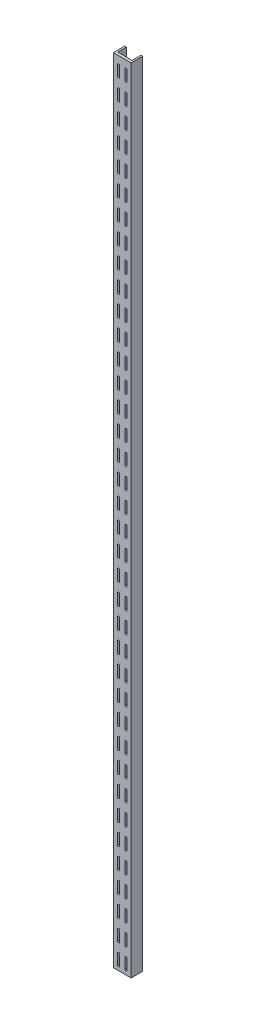
SolidWorks part; units mm, degrees
ref_plane "Front Plane" through (0, 0, 0) normal (0, 0, 1) x (1, 0, 0)
ref_plane "Top Plane" through (0, 0, 0) normal (0, 1, 0) x (1, 0, 0)
ref_plane "Right Plane" through (0, 0, 0) normal (1, 0, 0) x (0, 0, -1)
sketch "Sketch1" plane through (0, 0, 0) normal (0, 1, 0) x (1, 0, 0)
  line L0 (0, 0) -> (0, 17.7)
  line L1 (0, 17.7) -> (2.62, 17.7)
  line L2 (2.62, 17.7) -> (2.62, 4.15)
  line L3 (2.62, 4.15) -> (24.7, 4.15)
  line L4 (24.7, 4.15) -> (24.7, 17.7)
  line L5 (24.7, 17.7) -> (27.32, 17.7)
  line L6 (27.32, 17.7) -> (27.32, 0)
  line L7 (27.32, 0) -> (0, 0)
  line L8 (13.66, 4.15) -> (13.66, 0) construction
  dimension "D1" = 27.32
  dimension "D2" = 17.7
  dimension "D3" = 2.62
  dimension "D4" = 4.15
extrude "Boss-Extrude1" add sketch "Sketch1" along normal blind 1219.2
sketch "Sketch2" plane through (0, 0, -4.15) normal (0, 0, -1) x (-1, 0, 0)
  line L0 (-13.66, 1164.6545) -> (-13.66, 1127.3259) construction
  line L1 (-14.98, 1155.99) -> (-12.34, 1155.99)
  line L2 (-14.98, 1155.99) -> (-14.98, 1141.99)
  line L3 (-14.98, 1141.99) -> (-12.34, 1141.99)
  line L4 (-12.34, 1155.99) -> (-12.34, 1141.99)
  line L6 (-24.7, 1219.2) -> (-2.62, 1219.2) construction
  line L7 (-14.98, 1130.89) -> (-14.98, 1116.89)
  line L8 (-14.98, 1130.89) -> (-12.34, 1130.89)
  line L9 (-12.34, 1130.89) -> (-12.34, 1116.89)
  line L10 (-14.98, 1116.89) -> (-12.34, 1116.89)
  line L11 (-14.98, 1105.79) -> (-14.98, 1091.79)
  line L12 (-14.98, 1105.79) -> (-12.34, 1105.79)
  line L13 (-12.34, 1105.79) -> (-12.34, 1091.79)
  line L14 (-14.98, 1091.79) -> (-12.34, 1091.79)
  line L15 (-14.98, 1080.69) -> (-14.98, 1066.69)
  line L16 (-14.98, 1080.69) -> (-12.34, 1080.69)
  line L17 (-12.34, 1080.69) -> (-12.34, 1066.69)
  line L18 (-14.98, 1066.69) -> (-12.34, 1066.69)
  line L19 (-14.98, 1055.59) -> (-14.98, 1041.59)
  line L20 (-14.98, 1055.59) -> (-12.34, 1055.59)
  line L21 (-12.34, 1055.59) -> (-12.34, 1041.59)
  line L22 (-14.98, 1041.59) -> (-12.34, 1041.59)
  line L23 (-14.98, 1030.49) -> (-14.98, 1016.49)
  line L24 (-14.98, 1030.49) -> (-12.34, 1030.49)
  line L25 (-12.34, 1030.49) -> (-12.34, 1016.49)
  line L26 (-14.98, 1016.49) -> (-12.34, 1016.49)
  line L27 (-14.98, 1005.39) -> (-14.98, 991.39)
  line L28 (-14.98, 1005.39) -> (-12.34, 1005.39)
  line L29 (-12.34, 1005.39) -> (-12.34, 991.39)
  line L30 (-14.98, 991.39) -> (-12.34, 991.39)
  line L31 (-14.98, 980.29) -> (-14.98, 966.29)
  line L32 (-14.98, 980.29) -> (-12.34, 980.29)
  line L33 (-12.34, 980.29) -> (-12.34, 966.29)
  line L34 (-14.98, 966.29) -> (-12.34, 966.29)
  line L35 (-14.98, 955.19) -> (-14.98, 941.19)
  line L36 (-14.98, 955.19) -> (-12.34, 955.19)
  line L37 (-12.34, 955.19) -> (-12.34, 941.19)
  line L38 (-14.98, 941.19) -> (-12.34, 941.19)
  line L39 (-14.98, 930.09) -> (-14.98, 916.09)
  line L40 (-14.98, 930.09) -> (-12.34, 930.09)
  line L41 (-12.34, 930.09) -> (-12.34, 916.09)
  line L42 (-14.98, 916.09) -> (-12.34, 916.09)
  line L43 (-14.98, 904.99) -> (-14.98, 890.99)
  line L44 (-14.98, 904.99) -> (-12.34, 904.99)
  line L45 (-12.34, 904.99) -> (-12.34, 890.99)
  line L46 (-14.98, 890.99) -> (-12.34, 890.99)
  line L47 (-14.98, 879.89) -> (-14.98, 865.89)
  line L48 (-14.98, 879.89) -> (-12.34, 879.89)
  line L49 (-12.34, 879.89) -> (-12.34, 865.89)
  line L50 (-14.98, 865.89) -> (-12.34, 865.89)
  line L51 (-14.98, 854.79) -> (-14.98, 840.79)
  line L52 (-14.98, 854.79) -> (-12.34, 854.79)
  line L53 (-12.34, 854.79) -> (-12.34, 840.79)
  line L54 (-14.98, 840.79) -> (-12.34, 840.79)
  line L55 (-14.98, 829.69) -> (-14.98, 815.69)
  line L56 (-14.98, 829.69) -> (-12.34, 829.69)
  line L57 (-12.34, 829.69) -> (-12.34, 815.69)
  line L58 (-14.98, 815.69) -> (-12.34, 815.69)
  line L59 (-14.98, 804.59) -> (-14.98, 790.59)
  line L60 (-14.98, 804.59) -> (-12.34, 804.59)
  line L61 (-12.34, 804.59) -> (-12.34, 790.59)
  line L62 (-14.98, 790.59) -> (-12.34, 790.59)
  line L63 (-14.98, 779.49) -> (-14.98, 765.49)
  line L64 (-14.98, 779.49) -> (-12.34, 779.49)
  line L65 (-12.34, 779.49) -> (-12.34, 765.49)
  line L66 (-14.98, 765.49) -> (-12.34, 765.49)
  line L67 (-14.98, 754.39) -> (-14.98, 740.39)
  line L68 (-14.98, 754.39) -> (-12.34, 754.39)
  line L69 (-12.34, 754.39) -> (-12.34, 740.39)
  line L70 (-14.98, 740.39) -> (-12.34, 740.39)
  line L71 (-14.98, 729.29) -> (-14.98, 715.29)
  line L72 (-14.98, 729.29) -> (-12.34, 729.29)
  line L73 (-12.34, 729.29) -> (-12.34, 715.29)
  line L74 (-14.98, 715.29) -> (-12.34, 715.29)
  line L75 (-14.98, 704.19) -> (-14.98, 690.19)
  line L76 (-14.98, 704.19) -> (-12.34, 704.19)
  line L77 (-12.34, 704.19) -> (-12.34, 690.19)
  line L78 (-14.98, 690.19) -> (-12.34, 690.19)
  line L79 (-14.98, 679.09) -> (-14.98, 665.09)
  line L80 (-14.98, 679.09) -> (-12.34, 679.09)
  line L81 (-12.34, 679.09) -> (-12.34, 665.09)
  line L82 (-14.98, 665.09) -> (-12.34, 665.09)
  line L83 (-14.98, 653.99) -> (-14.98, 639.99)
  line L84 (-14.98, 653.99) -> (-12.34, 653.99)
  line L85 (-12.34, 653.99) -> (-12.34, 639.99)
  line L86 (-14.98, 639.99) -> (-12.34, 639.99)
  line L87 (-14.98, 628.89) -> (-14.98, 614.89)
  line L88 (-14.98, 628.89) -> (-12.34, 628.89)
  line L89 (-12.34, 628.89) -> (-12.34, 614.89)
  line L90 (-14.98, 614.89) -> (-12.34, 614.89)
  line L91 (-14.98, 603.79) -> (-14.98, 589.79)
  line L92 (-14.98, 603.79) -> (-12.34, 603.79)
  line L93 (-12.34, 603.79) -> (-12.34, 589.79)
  line L94 (-14.98, 589.79) -> (-12.34, 589.79)
  line L95 (-14.98, 578.69) -> (-14.98, 564.69)
  line L96 (-14.98, 578.69) -> (-12.34, 578.69)
  line L97 (-12.34, 578.69) -> (-12.34, 564.69)
  line L98 (-14.98, 564.69) -> (-12.34, 564.69)
  line L99 (-14.98, 553.59) -> (-14.98, 539.59)
  line L100 (-14.98, 553.59) -> (-12.34, 553.59)
  line L101 (-12.34, 553.59) -> (-12.34, 539.59)
  line L102 (-14.98, 539.59) -> (-12.34, 539.59)
  line L103 (-14.98, 528.49) -> (-14.98, 514.49)
  line L104 (-14.98, 528.49) -> (-12.34, 528.49)
  line L105 (-12.34, 528.49) -> (-12.34, 514.49)
  line L106 (-14.98, 514.49) -> (-12.34, 514.49)
  line L107 (-14.98, 503.39) -> (-14.98, 489.39)
  line L108 (-14.98, 503.39) -> (-12.34, 503.39)
  line L109 (-12.34, 503.39) -> (-12.34, 489.39)
  line L110 (-14.98, 489.39) -> (-12.34, 489.39)
  line L111 (-14.98, 478.29) -> (-14.98, 464.29)
  line L112 (-14.98, 478.29) -> (-12.34, 478.29)
  line L113 (-12.34, 478.29) -> (-12.34, 464.29)
  line L114 (-14.98, 464.29) -> (-12.34, 464.29)
  line L115 (-14.98, 453.19) -> (-14.98, 439.19)
  line L116 (-14.98, 453.19) -> (-12.34, 453.19)
  line L117 (-12.34, 453.19) -> (-12.34, 439.19)
  line L118 (-14.98, 439.19) -> (-12.34, 439.19)
  line L119 (-14.98, 428.09) -> (-14.98, 414.09)
  line L120 (-14.98, 428.09) -> (-12.34, 428.09)
  line L121 (-12.34, 428.09) -> (-12.34, 414.09)
  line L122 (-14.98, 414.09) -> (-12.34, 414.09)
  line L123 (-14.98, 402.99) -> (-14.98, 388.99)
  line L124 (-14.98, 402.99) -> (-12.34, 402.99)
  line L125 (-12.34, 402.99) -> (-12.34, 388.99)
  line L126 (-14.98, 388.99) -> (-12.34, 388.99)
  line L127 (-14.98, 377.89) -> (-14.98, 363.89)
  line L128 (-14.98, 377.89) -> (-12.34, 377.89)
  line L129 (-12.34, 377.89) -> (-12.34, 363.89)
  line L130 (-14.98, 363.89) -> (-12.34, 363.89)
  line L131 (-14.98, 352.79) -> (-14.98, 338.79)
  line L132 (-14.98, 352.79) -> (-12.34, 352.79)
  line L133 (-12.34, 352.79) -> (-12.34, 338.79)
  line L134 (-14.98, 338.79) -> (-12.34, 338.79)
  line L135 (-14.98, 327.69) -> (-14.98, 313.69)
  line L136 (-14.98, 327.69) -> (-12.34, 327.69)
  line L137 (-12.34, 327.69) -> (-12.34, 313.69)
  line L138 (-14.98, 313.69) -> (-12.34, 313.69)
  line L139 (-14.98, 302.59) -> (-14.98, 288.59)
  line L140 (-14.98, 302.59) -> (-12.34, 302.59)
  line L141 (-12.34, 302.59) -> (-12.34, 288.59)
  line L142 (-14.98, 288.59) -> (-12.34, 288.59)
  line L143 (-14.98, 277.49) -> (-14.98, 263.49)
  line L144 (-14.98, 277.49) -> (-12.34, 277.49)
  line L145 (-12.34, 277.49) -> (-12.34, 263.49)
  line L146 (-14.98, 263.49) -> (-12.34, 263.49)
  line L147 (-14.98, 252.39) -> (-14.98, 238.39)
  line L148 (-14.98, 252.39) -> (-12.34, 252.39)
  line L149 (-12.34, 252.39) -> (-12.34, 238.39)
  line L150 (-14.98, 238.39) -> (-12.34, 238.39)
  line L151 (-14.98, 227.29) -> (-14.98, 213.29)
  line L152 (-14.98, 227.29) -> (-12.34, 227.29)
  line L153 (-12.34, 227.29) -> (-12.34, 213.29)
  line L154 (-14.98, 213.29) -> (-12.34, 213.29)
  line L155 (-14.98, 202.19) -> (-14.98, 188.19)
  line L156 (-14.98, 202.19) -> (-12.34, 202.19)
  line L157 (-12.34, 202.19) -> (-12.34, 188.19)
  line L158 (-14.98, 188.19) -> (-12.34, 188.19)
  line L159 (-14.98, 177.09) -> (-14.98, 163.09)
  line L160 (-14.98, 177.09) -> (-12.34, 177.09)
  line L161 (-12.34, 177.09) -> (-12.34, 163.09)
  line L162 (-14.98, 163.09) -> (-12.34, 163.09)
  line L163 (-14.98, 151.99) -> (-14.98, 137.99)
  line L164 (-14.98, 151.99) -> (-12.34, 151.99)
  line L165 (-12.34, 151.99) -> (-12.34, 137.99)
  line L166 (-14.98, 137.99) -> (-12.34, 137.99)
  line L167 (-14.98, 126.89) -> (-14.98, 112.89)
  line L168 (-14.98, 126.89) -> (-12.34, 126.89)
  line L169 (-12.34, 126.89) -> (-12.34, 112.89)
  line L170 (-14.98, 112.89) -> (-12.34, 112.89)
  line L171 (-14.98, 101.79) -> (-14.98, 87.79)
  line L172 (-14.98, 101.79) -> (-12.34, 101.79)
  line L173 (-12.34, 101.79) -> (-12.34, 87.79)
  line L174 (-14.98, 87.79) -> (-12.34, 87.79)
  line L175 (-14.98, 76.69) -> (-14.98, 62.69)
  line L176 (-14.98, 76.69) -> (-12.34, 76.69)
  line L177 (-12.34, 76.69) -> (-12.34, 62.69)
  line L178 (-14.98, 62.69) -> (-12.34, 62.69)
  line L179 (-14.98, 51.59) -> (-14.98, 37.59)
  line L180 (-14.98, 51.59) -> (-12.34, 51.59)
  line L181 (-12.34, 51.59) -> (-12.34, 37.59)
  line L182 (-14.98, 37.59) -> (-12.34, 37.59)
  line L183 (-14.98, 26.49) -> (-14.98, 12.49)
  line L184 (-14.98, 26.49) -> (-12.34, 26.49)
  line L185 (-12.34, 26.49) -> (-12.34, 12.49)
  line L186 (-14.98, 12.49) -> (-12.34, 12.49)
  point P5 (-13.66, 1155.99)
  point P9 (-13.66, 1219.2)
  dimension "D1" = 2.64
  dimension "D2" = 63.21
  dimension "D3" = 14
  dimension "D4" = 46
  dimension "D5" = 11.1
extrude "Cut-Extrude1" [suppressed] cut sketch "Sketch2" against normal through all
sketch "Sketch3" plane through (0, 0, -4.15) normal (0, 0, -1) x (-1, 0, 0)
  line L0 (-13.66, 1225.2426) -> (-13.66, 1213.1338) construction
  line L2 (-24.7, 1219.2) -> (-2.62, 1219.2) construction
  circle A0 centre (-13.66, 1210.325) radius 2.195
  circle A1 centre (-13.66, 830.595) radius 2.195
  circle A2 centre (-13.66, 563.895) radius 2.195
  circle A3 centre (-13.66, 297.195) radius 2.195
  circle A4 centre (-13.66, 30.495) radius 2.195
  point P3 (-13.66, 1219.1882)
  point P5 (-13.66, 1219.2)
  dimension "D1" = 4.39
  dimension "D3" = 379.73
  dimension "D4" = 4.39
  dimension "D2" = 8.875
  dimension "D5" = 4
extrude "Cut-Extrude2" [suppressed] cut sketch "Sketch3" against normal through all
sketch "Sketch4" plane through (0, 0, -4.15) normal (0, 0, -1) x (-1, 0, 0)
  line L0 (-19.4, 1206.81) -> (-19.4, 1190.81) construction
  line L1 (-17.9, 1206.81) -> (-17.9, 1190.81)
  line L2 (-20.9, 1206.81) -> (-20.9, 1190.81)
  line L3 (-13.66, 1219.2) -> (-13.66, 0) construction
  line L4 (-24.7, 1219.2) -> (-2.62, 1219.2) construction
  line L5 (-24.7, 0) -> (-2.62, 0) construction
  line L6 (-20.9, 1174.81) -> (-20.9, 1158.81)
  line L7 (-17.9, 1174.81) -> (-17.9, 1158.81)
  line L8 (-19.4, 1174.81) -> (-19.4, 1158.81) construction
  line L9 (-20.9, 1142.81) -> (-20.9, 1126.81)
  line L10 (-17.9, 1142.81) -> (-17.9, 1126.81)
  line L11 (-19.4, 1142.81) -> (-19.4, 1126.81) construction
  line L12 (-20.9, 1110.81) -> (-20.9, 1094.81)
  line L13 (-17.9, 1110.81) -> (-17.9, 1094.81)
  line L14 (-19.4, 1110.81) -> (-19.4, 1094.81) construction
  line L15 (-20.9, 1078.81) -> (-20.9, 1062.81)
  line L16 (-17.9, 1078.81) -> (-17.9, 1062.81)
  line L17 (-19.4, 1078.81) -> (-19.4, 1062.81) construction
  line L18 (-20.9, 1046.81) -> (-20.9, 1030.81)
  line L19 (-17.9, 1046.81) -> (-17.9, 1030.81)
  line L20 (-19.4, 1046.81) -> (-19.4, 1030.81) construction
  line L21 (-20.9, 1014.81) -> (-20.9, 998.81)
  line L22 (-17.9, 1014.81) -> (-17.9, 998.81)
  line L23 (-19.4, 1014.81) -> (-19.4, 998.81) construction
  line L24 (-20.9, 982.81) -> (-20.9, 966.81)
  line L25 (-17.9, 982.81) -> (-17.9, 966.81)
  line L26 (-19.4, 982.81) -> (-19.4, 966.81) construction
  line L27 (-20.9, 950.81) -> (-20.9, 934.81)
  line L28 (-17.9, 950.81) -> (-17.9, 934.81)
  line L29 (-19.4, 950.81) -> (-19.4, 934.81) construction
  line L30 (-20.9, 918.81) -> (-20.9, 902.81)
  line L31 (-17.9, 918.81) -> (-17.9, 902.81)
  line L32 (-19.4, 918.81) -> (-19.4, 902.81) construction
  line L33 (-20.9, 886.81) -> (-20.9, 870.81)
  line L34 (-17.9, 886.81) -> (-17.9, 870.81)
  line L35 (-19.4, 886.81) -> (-19.4, 870.81) construction
  line L36 (-20.9, 854.81) -> (-20.9, 838.81)
  line L37 (-17.9, 854.81) -> (-17.9, 838.81)
  line L38 (-19.4, 854.81) -> (-19.4, 838.81) construction
  line L39 (-20.9, 822.81) -> (-20.9, 806.81)
  line L40 (-17.9, 822.81) -> (-17.9, 806.81)
  line L41 (-19.4, 822.81) -> (-19.4, 806.81) construction
  line L42 (-20.9, 790.81) -> (-20.9, 774.81)
  line L43 (-17.9, 790.81) -> (-17.9, 774.81)
  line L44 (-19.4, 790.81) -> (-19.4, 774.81) construction
  line L45 (-20.9, 758.81) -> (-20.9, 742.81)
  line L46 (-17.9, 758.81) -> (-17.9, 742.81)
  line L47 (-19.4, 758.81) -> (-19.4, 742.81) construction
  line L48 (-20.9, 726.81) -> (-20.9, 710.81)
  line L49 (-17.9, 726.81) -> (-17.9, 710.81)
  line L50 (-19.4, 726.81) -> (-19.4, 710.81) construction
  line L51 (-20.9, 694.81) -> (-20.9, 678.81)
  line L52 (-17.9, 694.81) -> (-17.9, 678.81)
  line L53 (-19.4, 694.81) -> (-19.4, 678.81) construction
  line L54 (-20.9, 662.81) -> (-20.9, 646.81)
  line L55 (-17.9, 662.81) -> (-17.9, 646.81)
  line L56 (-19.4, 662.81) -> (-19.4, 646.81) construction
  line L57 (-20.9, 630.81) -> (-20.9, 614.81)
  line L58 (-17.9, 630.81) -> (-17.9, 614.81)
  line L59 (-19.4, 630.81) -> (-19.4, 614.81) construction
  line L60 (-20.9, 598.81) -> (-20.9, 582.81)
  line L61 (-17.9, 598.81) -> (-17.9, 582.81)
  line L62 (-19.4, 598.81) -> (-19.4, 582.81) construction
  line L63 (-20.9, 566.81) -> (-20.9, 550.81)
  line L64 (-17.9, 566.81) -> (-17.9, 550.81)
  line L65 (-19.4, 566.81) -> (-19.4, 550.81) construction
  line L66 (-20.9, 534.81) -> (-20.9, 518.81)
  line L67 (-17.9, 534.81) -> (-17.9, 518.81)
  line L68 (-19.4, 534.81) -> (-19.4, 518.81) construction
  line L69 (-20.9, 502.81) -> (-20.9, 486.81)
  line L70 (-17.9, 502.81) -> (-17.9, 486.81)
  line L71 (-19.4, 502.81) -> (-19.4, 486.81) construction
  line L72 (-20.9, 470.81) -> (-20.9, 454.81)
  line L73 (-17.9, 470.81) -> (-17.9, 454.81)
  line L74 (-19.4, 470.81) -> (-19.4, 454.81) construction
  line L75 (-20.9, 438.81) -> (-20.9, 422.81)
  line L76 (-17.9, 438.81) -> (-17.9, 422.81)
  line L77 (-19.4, 438.81) -> (-19.4, 422.81) construction
  line L78 (-20.9, 406.81) -> (-20.9, 390.81)
  line L79 (-17.9, 406.81) -> (-17.9, 390.81)
  line L80 (-19.4, 406.81) -> (-19.4, 390.81) construction
  line L81 (-20.9, 374.81) -> (-20.9, 358.81)
  line L82 (-17.9, 374.81) -> (-17.9, 358.81)
  line L83 (-19.4, 374.81) -> (-19.4, 358.81) construction
  line L84 (-20.9, 342.81) -> (-20.9, 326.81)
  line L85 (-17.9, 342.81) -> (-17.9, 326.81)
  line L86 (-19.4, 342.81) -> (-19.4, 326.81) construction
  line L87 (-20.9, 310.81) -> (-20.9, 294.81)
  line L88 (-17.9, 310.81) -> (-17.9, 294.81)
  line L89 (-19.4, 310.81) -> (-19.4, 294.81) construction
  line L90 (-20.9, 278.81) -> (-20.9, 262.81)
  line L91 (-17.9, 278.81) -> (-17.9, 262.81)
  line L92 (-19.4, 278.81) -> (-19.4, 262.81) construction
  line L93 (-20.9, 246.81) -> (-20.9, 230.81)
  line L94 (-17.9, 246.81) -> (-17.9, 230.81)
  line L95 (-19.4, 246.81) -> (-19.4, 230.81) construction
  line L96 (-20.9, 214.81) -> (-20.9, 198.81)
  line L97 (-17.9, 214.81) -> (-17.9, 198.81)
  line L98 (-19.4, 214.81) -> (-19.4, 198.81) construction
  line L99 (-20.9, 182.81) -> (-20.9, 166.81)
  line L100 (-17.9, 182.81) -> (-17.9, 166.81)
  line L101 (-19.4, 182.81) -> (-19.4, 166.81) construction
  line L102 (-20.9, 150.81) -> (-20.9, 134.81)
  line L103 (-17.9, 150.81) -> (-17.9, 134.81)
  line L104 (-19.4, 150.81) -> (-19.4, 134.81) construction
  line L105 (-20.9, 118.81) -> (-20.9, 102.81)
  line L106 (-17.9, 118.81) -> (-17.9, 102.81)
  line L107 (-19.4, 118.81) -> (-19.4, 102.81) construction
  line L108 (-20.9, 86.81) -> (-20.9, 70.81)
  line L109 (-17.9, 86.81) -> (-17.9, 70.81)
  line L110 (-19.4, 86.81) -> (-19.4, 70.81) construction
  line L111 (-20.9, 54.81) -> (-20.9, 38.81)
  line L112 (-17.9, 54.81) -> (-17.9, 38.81)
  line L113 (-19.4, 54.81) -> (-19.4, 38.81) construction
  line L114 (-20.9, 22.81) -> (-20.9, 6.81)
  line L115 (-17.9, 22.81) -> (-17.9, 6.81)
  line L116 (-19.4, 22.81) -> (-19.4, 6.81) construction
  line L117 (-7.92, 758.81) -> (-7.92, 742.81) construction
  line L118 (-9.42, 758.81) -> (-9.42, 742.81)
  line L119 (-6.42, 758.81) -> (-6.42, 742.81)
  line L120 (-7.92, 790.81) -> (-7.92, 774.81) construction
  line L121 (-9.42, 790.81) -> (-9.42, 774.81)
  line L122 (-6.42, 790.81) -> (-6.42, 774.81)
  line L123 (-7.92, 822.81) -> (-7.92, 806.81) construction
  line L124 (-9.42, 822.81) -> (-9.42, 806.81)
  line L125 (-6.42, 822.81) -> (-6.42, 806.81)
  line L126 (-7.92, 854.81) -> (-7.92, 838.81) construction
  line L127 (-9.42, 854.81) -> (-9.42, 838.81)
  line L128 (-6.42, 854.81) -> (-6.42, 838.81)
  line L129 (-7.92, 886.81) -> (-7.92, 870.81) construction
  line L130 (-9.42, 886.81) -> (-9.42, 870.81)
  line L131 (-6.42, 886.81) -> (-6.42, 870.81)
  line L132 (-7.92, 918.81) -> (-7.92, 902.81) construction
  line L133 (-9.42, 918.81) -> (-9.42, 902.81)
  line L134 (-6.42, 918.81) -> (-6.42, 902.81)
  line L135 (-7.92, 950.81) -> (-7.92, 934.81) construction
  line L136 (-9.42, 950.81) -> (-9.42, 934.81)
  line L137 (-6.42, 950.81) -> (-6.42, 934.81)
  line L138 (-7.92, 982.81) -> (-7.92, 966.81) construction
  line L139 (-9.42, 982.81) -> (-9.42, 966.81)
  line L140 (-6.42, 982.81) -> (-6.42, 966.81)
  line L141 (-7.92, 1014.81) -> (-7.92, 998.81) construction
  line L142 (-9.42, 1014.81) -> (-9.42, 998.81)
  line L143 (-6.42, 1014.81) -> (-6.42, 998.81)
  line L144 (-7.92, 1046.81) -> (-7.92, 1030.81) construction
  line L145 (-9.42, 1046.81) -> (-9.42, 1030.81)
  line L146 (-6.42, 1046.81) -> (-6.42, 1030.81)
  line L147 (-7.92, 1078.81) -> (-7.92, 1062.81) construction
  line L148 (-9.42, 1078.81) -> (-9.42, 1062.81)
  line L149 (-6.42, 1078.81) -> (-6.42, 1062.81)
  line L150 (-7.92, 1110.81) -> (-7.92, 1094.81) construction
  line L151 (-9.42, 1110.81) -> (-9.42, 1094.81)
  line L152 (-6.42, 1110.81) -> (-6.42, 1094.81)
  line L153 (-7.92, 1142.81) -> (-7.92, 1126.81) construction
  line L154 (-9.42, 1142.81) -> (-9.42, 1126.81)
  line L155 (-6.42, 1142.81) -> (-6.42, 1126.81)
  line L156 (-7.92, 1174.81) -> (-7.92, 1158.81) construction
  line L157 (-9.42, 1174.81) -> (-9.42, 1158.81)
  line L158 (-6.42, 1174.81) -> (-6.42, 1158.81)
  line L159 (-7.92, 1206.81) -> (-7.92, 1190.81) construction
  line L160 (-9.42, 1206.81) -> (-9.42, 1190.81)
  line L161 (-6.42, 1206.81) -> (-6.42, 1190.81)
  line L162 (-7.92, 406.81) -> (-7.92, 390.81) construction
  line L163 (-9.42, 406.81) -> (-9.42, 390.81)
  line L164 (-6.42, 406.81) -> (-6.42, 390.81)
  line L165 (-7.92, 438.81) -> (-7.92, 422.81) construction
  line L166 (-9.42, 438.81) -> (-9.42, 422.81)
  line L167 (-6.42, 438.81) -> (-6.42, 422.81)
  line L168 (-7.92, 470.81) -> (-7.92, 454.81) construction
  line L169 (-9.42, 470.81) -> (-9.42, 454.81)
  line L170 (-6.42, 470.81) -> (-6.42, 454.81)
  line L171 (-7.92, 502.81) -> (-7.92, 486.81) construction
  line L172 (-9.42, 502.81) -> (-9.42, 486.81)
  line L173 (-6.42, 502.81) -> (-6.42, 486.81)
  line L174 (-7.92, 534.81) -> (-7.92, 518.81) construction
  line L175 (-9.42, 534.81) -> (-9.42, 518.81)
  line L176 (-6.42, 534.81) -> (-6.42, 518.81)
  line L177 (-7.92, 566.81) -> (-7.92, 550.81) construction
  line L178 (-9.42, 566.81) -> (-9.42, 550.81)
  line L179 (-6.42, 566.81) -> (-6.42, 550.81)
  line L180 (-7.92, 598.81) -> (-7.92, 582.81) construction
  line L181 (-9.42, 598.81) -> (-9.42, 582.81)
  line L182 (-6.42, 598.81) -> (-6.42, 582.81)
  line L183 (-7.92, 630.81) -> (-7.92, 614.81) construction
  line L184 (-9.42, 630.81) -> (-9.42, 614.81)
  line L185 (-6.42, 630.81) -> (-6.42, 614.81)
  line L186 (-7.92, 662.81) -> (-7.92, 646.81) construction
  line L187 (-9.42, 662.81) -> (-9.42, 646.81)
  line L188 (-6.42, 662.81) -> (-6.42, 646.81)
  line L189 (-7.92, 694.81) -> (-7.92, 678.81) construction
  line L190 (-9.42, 694.81) -> (-9.42, 678.81)
  line L191 (-6.42, 694.81) -> (-6.42, 678.81)
  line L192 (-7.92, 726.81) -> (-7.92, 710.81) construction
  line L193 (-9.42, 726.81) -> (-9.42, 710.81)
  line L194 (-6.42, 726.81) -> (-6.42, 710.81)
  line L195 (-7.92, 374.81) -> (-7.92, 358.81) construction
  line L196 (-9.42, 374.81) -> (-9.42, 358.81)
  line L197 (-6.42, 374.81) -> (-6.42, 358.81)
  line L198 (-7.92, 342.81) -> (-7.92, 326.81) construction
  line L199 (-9.42, 342.81) -> (-9.42, 326.81)
  line L200 (-6.42, 342.81) -> (-6.42, 326.81)
  line L201 (-7.92, 310.81) -> (-7.92, 294.81) construction
  line L202 (-9.42, 310.81) -> (-9.42, 294.81)
  line L203 (-6.42, 310.81) -> (-6.42, 294.81)
  line L204 (-7.92, 278.81) -> (-7.92, 262.81) construction
  line L205 (-9.42, 278.81) -> (-9.42, 262.81)
  line L206 (-6.42, 278.81) -> (-6.42, 262.81)
  line L207 (-7.92, 246.81) -> (-7.92, 230.81) construction
  line L208 (-9.42, 246.81) -> (-9.42, 230.81)
  line L209 (-6.42, 246.81) -> (-6.42, 230.81)
  line L210 (-7.92, 214.81) -> (-7.92, 198.81) construction
  line L211 (-9.42, 214.81) -> (-9.42, 198.81)
  line L212 (-6.42, 214.81) -> (-6.42, 198.81)
  line L213 (-7.92, 182.81) -> (-7.92, 166.81) construction
  line L214 (-9.42, 182.81) -> (-9.42, 166.81)
  line L215 (-6.42, 182.81) -> (-6.42, 166.81)
  line L216 (-7.92, 150.81) -> (-7.92, 134.81) construction
  line L217 (-9.42, 150.81) -> (-9.42, 134.81)
  line L218 (-6.42, 150.81) -> (-6.42, 134.81)
  line L219 (-7.92, 118.81) -> (-7.92, 102.81) construction
  line L220 (-9.42, 118.81) -> (-9.42, 102.81)
  line L221 (-6.42, 118.81) -> (-6.42, 102.81)
  line L222 (-7.92, 86.81) -> (-7.92, 70.81) construction
  line L223 (-9.42, 86.81) -> (-9.42, 70.81)
  line L224 (-6.42, 86.81) -> (-6.42, 70.81)
  line L225 (-7.92, 54.81) -> (-7.92, 38.81) construction
  line L226 (-9.42, 54.81) -> (-9.42, 38.81)
  line L227 (-6.42, 54.81) -> (-6.42, 38.81)
  line L228 (-7.92, 22.81) -> (-7.92, 6.81) construction
  line L229 (-9.42, 22.81) -> (-9.42, 6.81)
  line L230 (-6.42, 22.81) -> (-6.42, 6.81)
  arc A0 (-17.9, 1206.81) -> (-20.9, 1206.81) centre (-19.4, 1206.81) ccw
  arc A1 (-20.9, 1190.81) -> (-17.9, 1190.81) centre (-19.4, 1190.81) ccw
  arc A2 (-17.9, 1174.81) -> (-20.9, 1174.81) centre (-19.4, 1174.81) ccw
  arc A3 (-20.9, 1158.81) -> (-17.9, 1158.81) centre (-19.4, 1158.81) ccw
  arc A4 (-17.9, 1142.81) -> (-20.9, 1142.81) centre (-19.4, 1142.81) ccw
  arc A5 (-20.9, 1126.81) -> (-17.9, 1126.81) centre (-19.4, 1126.81) ccw
  arc A6 (-17.9, 1110.81) -> (-20.9, 1110.81) centre (-19.4, 1110.81) ccw
  arc A7 (-20.9, 1094.81) -> (-17.9, 1094.81) centre (-19.4, 1094.81) ccw
  arc A8 (-17.9, 1078.81) -> (-20.9, 1078.81) centre (-19.4, 1078.81) ccw
  arc A9 (-20.9, 1062.81) -> (-17.9, 1062.81) centre (-19.4, 1062.81) ccw
  arc A10 (-17.9, 1046.81) -> (-20.9, 1046.81) centre (-19.4, 1046.81) ccw
  arc A11 (-20.9, 1030.81) -> (-17.9, 1030.81) centre (-19.4, 1030.81) ccw
  arc A12 (-17.9, 1014.81) -> (-20.9, 1014.81) centre (-19.4, 1014.81) ccw
  arc A13 (-20.9, 998.81) -> (-17.9, 998.81) centre (-19.4, 998.81) ccw
  arc A14 (-17.9, 982.81) -> (-20.9, 982.81) centre (-19.4, 982.81) ccw
  arc A15 (-20.9, 966.81) -> (-17.9, 966.81) centre (-19.4, 966.81) ccw
  arc A16 (-17.9, 950.81) -> (-20.9, 950.81) centre (-19.4, 950.81) ccw
  arc A17 (-20.9, 934.81) -> (-17.9, 934.81) centre (-19.4, 934.81) ccw
  arc A18 (-17.9, 918.81) -> (-20.9, 918.81) centre (-19.4, 918.81) ccw
  arc A19 (-20.9, 902.81) -> (-17.9, 902.81) centre (-19.4, 902.81) ccw
  arc A20 (-17.9, 886.81) -> (-20.9, 886.81) centre (-19.4, 886.81) ccw
  arc A21 (-20.9, 870.81) -> (-17.9, 870.81) centre (-19.4, 870.81) ccw
  arc A22 (-17.9, 854.81) -> (-20.9, 854.81) centre (-19.4, 854.81) ccw
  arc A23 (-20.9, 838.81) -> (-17.9, 838.81) centre (-19.4, 838.81) ccw
  arc A24 (-17.9, 822.81) -> (-20.9, 822.81) centre (-19.4, 822.81) ccw
  arc A25 (-20.9, 806.81) -> (-17.9, 806.81) centre (-19.4, 806.81) ccw
  arc A26 (-17.9, 790.81) -> (-20.9, 790.81) centre (-19.4, 790.81) ccw
  arc A27 (-20.9, 774.81) -> (-17.9, 774.81) centre (-19.4, 774.81) ccw
  arc A28 (-17.9, 758.81) -> (-20.9, 758.81) centre (-19.4, 758.81) ccw
  arc A29 (-20.9, 742.81) -> (-17.9, 742.81) centre (-19.4, 742.81) ccw
  arc A30 (-17.9, 726.81) -> (-20.9, 726.81) centre (-19.4, 726.81) ccw
  arc A31 (-20.9, 710.81) -> (-17.9, 710.81) centre (-19.4, 710.81) ccw
  arc A32 (-17.9, 694.81) -> (-20.9, 694.81) centre (-19.4, 694.81) ccw
  arc A33 (-20.9, 678.81) -> (-17.9, 678.81) centre (-19.4, 678.81) ccw
  arc A34 (-17.9, 662.81) -> (-20.9, 662.81) centre (-19.4, 662.81) ccw
  arc A35 (-20.9, 646.81) -> (-17.9, 646.81) centre (-19.4, 646.81) ccw
  arc A36 (-17.9, 630.81) -> (-20.9, 630.81) centre (-19.4, 630.81) ccw
  arc A37 (-20.9, 614.81) -> (-17.9, 614.81) centre (-19.4, 614.81) ccw
  arc A38 (-17.9, 598.81) -> (-20.9, 598.81) centre (-19.4, 598.81) ccw
  arc A39 (-20.9, 582.81) -> (-17.9, 582.81) centre (-19.4, 582.81) ccw
  arc A40 (-17.9, 566.81) -> (-20.9, 566.81) centre (-19.4, 566.81) ccw
  arc A41 (-20.9, 550.81) -> (-17.9, 550.81) centre (-19.4, 550.81) ccw
  arc A42 (-17.9, 534.81) -> (-20.9, 534.81) centre (-19.4, 534.81) ccw
  arc A43 (-20.9, 518.81) -> (-17.9, 518.81) centre (-19.4, 518.81) ccw
  arc A44 (-17.9, 502.81) -> (-20.9, 502.81) centre (-19.4, 502.81) ccw
  arc A45 (-20.9, 486.81) -> (-17.9, 486.81) centre (-19.4, 486.81) ccw
  arc A46 (-17.9, 470.81) -> (-20.9, 470.81) centre (-19.4, 470.81) ccw
  arc A47 (-20.9, 454.81) -> (-17.9, 454.81) centre (-19.4, 454.81) ccw
  arc A48 (-17.9, 438.81) -> (-20.9, 438.81) centre (-19.4, 438.81) ccw
  arc A49 (-20.9, 422.81) -> (-17.9, 422.81) centre (-19.4, 422.81) ccw
  arc A50 (-17.9, 406.81) -> (-20.9, 406.81) centre (-19.4, 406.81) ccw
  arc A51 (-20.9, 390.81) -> (-17.9, 390.81) centre (-19.4, 390.81) ccw
  arc A52 (-17.9, 374.81) -> (-20.9, 374.81) centre (-19.4, 374.81) ccw
  arc A53 (-20.9, 358.81) -> (-17.9, 358.81) centre (-19.4, 358.81) ccw
  arc A54 (-17.9, 342.81) -> (-20.9, 342.81) centre (-19.4, 342.81) ccw
  arc A55 (-20.9, 326.81) -> (-17.9, 326.81) centre (-19.4, 326.81) ccw
  arc A56 (-17.9, 310.81) -> (-20.9, 310.81) centre (-19.4, 310.81) ccw
  arc A57 (-20.9, 294.81) -> (-17.9, 294.81) centre (-19.4, 294.81) ccw
  arc A58 (-17.9, 278.81) -> (-20.9, 278.81) centre (-19.4, 278.81) ccw
  arc A59 (-20.9, 262.81) -> (-17.9, 262.81) centre (-19.4, 262.81) ccw
  arc A60 (-17.9, 246.81) -> (-20.9, 246.81) centre (-19.4, 246.81) ccw
  arc A61 (-20.9, 230.81) -> (-17.9, 230.81) centre (-19.4, 230.81) ccw
  arc A62 (-17.9, 214.81) -> (-20.9, 214.81) centre (-19.4, 214.81) ccw
  arc A63 (-20.9, 198.81) -> (-17.9, 198.81) centre (-19.4, 198.81) ccw
  arc A64 (-17.9, 182.81) -> (-20.9, 182.81) centre (-19.4, 182.81) ccw
  arc A65 (-20.9, 166.81) -> (-17.9, 166.81) centre (-19.4, 166.81) ccw
  arc A66 (-17.9, 150.81) -> (-20.9, 150.81) centre (-19.4, 150.81) ccw
  arc A67 (-20.9, 134.81) -> (-17.9, 134.81) centre (-19.4, 134.81) ccw
  arc A68 (-17.9, 118.81) -> (-20.9, 118.81) centre (-19.4, 118.81) ccw
  arc A69 (-20.9, 102.81) -> (-17.9, 102.81) centre (-19.4, 102.81) ccw
  arc A70 (-17.9, 86.81) -> (-20.9, 86.81) centre (-19.4, 86.81) ccw
  arc A71 (-20.9, 70.81) -> (-17.9, 70.81) centre (-19.4, 70.81) ccw
  arc A72 (-17.9, 54.81) -> (-20.9, 54.81) centre (-19.4, 54.81) ccw
  arc A73 (-20.9, 38.81) -> (-17.9, 38.81) centre (-19.4, 38.81) ccw
  arc A74 (-17.9, 22.81) -> (-20.9, 22.81) centre (-19.4, 22.81) ccw
  arc A75 (-20.9, 6.81) -> (-17.9, 6.81) centre (-19.4, 6.81) ccw
  arc A76 (-9.42, 758.81) -> (-6.42, 758.81) centre (-7.92, 758.81) cw
  arc A77 (-6.42, 742.81) -> (-9.42, 742.81) centre (-7.92, 742.81) cw
  arc A78 (-9.42, 790.81) -> (-6.42, 790.81) centre (-7.92, 790.81) cw
  arc A79 (-6.42, 774.81) -> (-9.42, 774.81) centre (-7.92, 774.81) cw
  arc A80 (-9.42, 822.81) -> (-6.42, 822.81) centre (-7.92, 822.81) cw
  arc A81 (-6.42, 806.81) -> (-9.42, 806.81) centre (-7.92, 806.81) cw
  arc A82 (-9.42, 854.81) -> (-6.42, 854.81) centre (-7.92, 854.81) cw
  arc A83 (-6.42, 838.81) -> (-9.42, 838.81) centre (-7.92, 838.81) cw
  arc A84 (-9.42, 886.81) -> (-6.42, 886.81) centre (-7.92, 886.81) cw
  arc A85 (-6.42, 870.81) -> (-9.42, 870.81) centre (-7.92, 870.81) cw
  arc A86 (-9.42, 918.81) -> (-6.42, 918.81) centre (-7.92, 918.81) cw
  arc A87 (-6.42, 902.81) -> (-9.42, 902.81) centre (-7.92, 902.81) cw
  arc A88 (-9.42, 950.81) -> (-6.42, 950.81) centre (-7.92, 950.81) cw
  arc A89 (-6.42, 934.81) -> (-9.42, 934.81) centre (-7.92, 934.81) cw
  arc A90 (-9.42, 982.81) -> (-6.42, 982.81) centre (-7.92, 982.81) cw
  arc A91 (-6.42, 966.81) -> (-9.42, 966.81) centre (-7.92, 966.81) cw
  arc A92 (-9.42, 1014.81) -> (-6.42, 1014.81) centre (-7.92, 1014.81) cw
  arc A93 (-6.42, 998.81) -> (-9.42, 998.81) centre (-7.92, 998.81) cw
  arc A94 (-9.42, 1046.81) -> (-6.42, 1046.81) centre (-7.92, 1046.81) cw
  arc A95 (-6.42, 1030.81) -> (-9.42, 1030.81) centre (-7.92, 1030.81) cw
  arc A96 (-9.42, 1078.81) -> (-6.42, 1078.81) centre (-7.92, 1078.81) cw
  arc A97 (-6.42, 1062.81) -> (-9.42, 1062.81) centre (-7.92, 1062.81) cw
  arc A98 (-9.42, 1110.81) -> (-6.42, 1110.81) centre (-7.92, 1110.81) cw
  arc A99 (-6.42, 1094.81) -> (-9.42, 1094.81) centre (-7.92, 1094.81) cw
  arc A100 (-9.42, 1142.81) -> (-6.42, 1142.81) centre (-7.92, 1142.81) cw
  arc A101 (-6.42, 1126.81) -> (-9.42, 1126.81) centre (-7.92, 1126.81) cw
  arc A102 (-9.42, 1174.81) -> (-6.42, 1174.81) centre (-7.92, 1174.81) cw
  arc A103 (-6.42, 1158.81) -> (-9.42, 1158.81) centre (-7.92, 1158.81) cw
  arc A104 (-9.42, 1206.81) -> (-6.42, 1206.81) centre (-7.92, 1206.81) cw
  arc A105 (-6.42, 1190.81) -> (-9.42, 1190.81) centre (-7.92, 1190.81) cw
  arc A106 (-9.42, 406.81) -> (-6.42, 406.81) centre (-7.92, 406.81) cw
  arc A107 (-6.42, 390.81) -> (-9.42, 390.81) centre (-7.92, 390.81) cw
  arc A108 (-9.42, 438.81) -> (-6.42, 438.81) centre (-7.92, 438.81) cw
  arc A109 (-6.42, 422.81) -> (-9.42, 422.81) centre (-7.92, 422.81) cw
  arc A110 (-9.42, 470.81) -> (-6.42, 470.81) centre (-7.92, 470.81) cw
  arc A111 (-6.42, 454.81) -> (-9.42, 454.81) centre (-7.92, 454.81) cw
  arc A112 (-9.42, 502.81) -> (-6.42, 502.81) centre (-7.92, 502.81) cw
  arc A113 (-6.42, 486.81) -> (-9.42, 486.81) centre (-7.92, 486.81) cw
  arc A114 (-9.42, 534.81) -> (-6.42, 534.81) centre (-7.92, 534.81) cw
  arc A115 (-6.42, 518.81) -> (-9.42, 518.81) centre (-7.92, 518.81) cw
  arc A116 (-9.42, 566.81) -> (-6.42, 566.81) centre (-7.92, 566.81) cw
  arc A117 (-6.42, 550.81) -> (-9.42, 550.81) centre (-7.92, 550.81) cw
  arc A118 (-9.42, 598.81) -> (-6.42, 598.81) centre (-7.92, 598.81) cw
  arc A119 (-6.42, 582.81) -> (-9.42, 582.81) centre (-7.92, 582.81) cw
  arc A120 (-9.42, 630.81) -> (-6.42, 630.81) centre (-7.92, 630.81) cw
  arc A121 (-6.42, 614.81) -> (-9.42, 614.81) centre (-7.92, 614.81) cw
  arc A122 (-9.42, 662.81) -> (-6.42, 662.81) centre (-7.92, 662.81) cw
  arc A123 (-6.42, 646.81) -> (-9.42, 646.81) centre (-7.92, 646.81) cw
  arc A124 (-9.42, 694.81) -> (-6.42, 694.81) centre (-7.92, 694.81) cw
  arc A125 (-6.42, 678.81) -> (-9.42, 678.81) centre (-7.92, 678.81) cw
  arc A126 (-9.42, 726.81) -> (-6.42, 726.81) centre (-7.92, 726.81) cw
  arc A127 (-6.42, 710.81) -> (-9.42, 710.81) centre (-7.92, 710.81) cw
  arc A128 (-9.42, 374.81) -> (-6.42, 374.81) centre (-7.92, 374.81) cw
  arc A129 (-6.42, 358.81) -> (-9.42, 358.81) centre (-7.92, 358.81) cw
  arc A130 (-9.42, 342.81) -> (-6.42, 342.81) centre (-7.92, 342.81) cw
  arc A131 (-6.42, 326.81) -> (-9.42, 326.81) centre (-7.92, 326.81) cw
  arc A132 (-9.42, 310.81) -> (-6.42, 310.81) centre (-7.92, 310.81) cw
  arc A133 (-6.42, 294.81) -> (-9.42, 294.81) centre (-7.92, 294.81) cw
  arc A134 (-9.42, 278.81) -> (-6.42, 278.81) centre (-7.92, 278.81) cw
  arc A135 (-6.42, 262.81) -> (-9.42, 262.81) centre (-7.92, 262.81) cw
  arc A136 (-9.42, 246.81) -> (-6.42, 246.81) centre (-7.92, 246.81) cw
  arc A137 (-6.42, 230.81) -> (-9.42, 230.81) centre (-7.92, 230.81) cw
  arc A138 (-9.42, 214.81) -> (-6.42, 214.81) centre (-7.92, 214.81) cw
  arc A139 (-6.42, 198.81) -> (-9.42, 198.81) centre (-7.92, 198.81) cw
  arc A140 (-9.42, 182.81) -> (-6.42, 182.81) centre (-7.92, 182.81) cw
  arc A141 (-6.42, 166.81) -> (-9.42, 166.81) centre (-7.92, 166.81) cw
  arc A142 (-9.42, 150.81) -> (-6.42, 150.81) centre (-7.92, 150.81) cw
  arc A143 (-6.42, 134.81) -> (-9.42, 134.81) centre (-7.92, 134.81) cw
  arc A144 (-9.42, 118.81) -> (-6.42, 118.81) centre (-7.92, 118.81) cw
  arc A145 (-6.42, 102.81) -> (-9.42, 102.81) centre (-7.92, 102.81) cw
  arc A146 (-9.42, 86.81) -> (-6.42, 86.81) centre (-7.92, 86.81) cw
  arc A147 (-6.42, 70.81) -> (-9.42, 70.81) centre (-7.92, 70.81) cw
  arc A148 (-9.42, 54.81) -> (-6.42, 54.81) centre (-7.92, 54.81) cw
  arc A149 (-6.42, 38.81) -> (-9.42, 38.81) centre (-7.92, 38.81) cw
  arc A150 (-9.42, 22.81) -> (-6.42, 22.81) centre (-7.92, 22.81) cw
  arc A151 (-6.42, 6.81) -> (-9.42, 6.81) centre (-7.92, 6.81) cw
  point P2 (-19.4, 1198.81)
  point P16 (-19.4, 1166.81)
  point P23 (-19.4, 1134.81)
  point P30 (-19.4, 1102.81)
  point P37 (-19.4, 1070.81)
  point P44 (-19.4, 1038.81)
  point P51 (-19.4, 1006.81)
  point P58 (-19.4, 974.81)
  point P65 (-19.4, 942.81)
  point P72 (-19.4, 910.81)
  point P79 (-19.4, 878.81)
  point P86 (-19.4, 846.81)
  point P93 (-19.4, 814.81)
  point P100 (-19.4, 782.81)
  point P107 (-19.4, 750.81)
  point P114 (-19.4, 718.81)
  point P121 (-19.4, 686.81)
  point P128 (-19.4, 654.81)
  point P135 (-19.4, 622.81)
  point P142 (-19.4, 590.81)
  point P149 (-19.4, 558.81)
  point P156 (-19.4, 526.81)
  point P163 (-19.4, 494.81)
  point P170 (-19.4, 462.81)
  point P177 (-19.4, 430.81)
  point P184 (-19.4, 398.81)
  point P191 (-19.4, 366.81)
  point P198 (-19.4, 334.81)
  point P205 (-19.4, 302.81)
  point P212 (-19.4, 270.81)
  point P219 (-19.4, 238.81)
  point P226 (-19.4, 206.81)
  point P233 (-19.4, 174.81)
  point P240 (-19.4, 142.81)
  point P247 (-19.4, 110.81)
  point P254 (-19.4, 78.81)
  point P261 (-19.4, 46.81)
  point P268 (-19.4, 14.81)
  point P274 (-7.92, 750.81)
  point P281 (-7.92, 782.81)
  point P288 (-7.92, 814.81)
  point P295 (-7.92, 846.81)
  point P302 (-7.92, 878.81)
  point P309 (-7.92, 910.81)
  point P316 (-7.92, 942.81)
  point P323 (-7.92, 974.81)
  point P330 (-7.92, 1006.81)
  point P337 (-7.92, 1038.81)
  point P344 (-7.92, 1070.81)
  point P351 (-7.92, 1102.81)
  point P358 (-7.92, 1134.81)
  point P365 (-7.92, 1166.81)
  point P372 (-7.92, 1198.81)
  point P379 (-7.92, 398.81)
  point P386 (-7.92, 430.81)
  point P393 (-7.92, 462.81)
  point P400 (-7.92, 494.81)
  point P407 (-7.92, 526.81)
  point P414 (-7.92, 558.81)
  point P421 (-7.92, 590.81)
  point P428 (-7.92, 622.81)
  point P435 (-7.92, 654.81)
  point P442 (-7.92, 686.81)
  point P449 (-7.92, 718.81)
  point P456 (-7.92, 366.81)
  point P463 (-7.92, 334.81)
  point P470 (-7.92, 302.81)
  point P477 (-7.92, 270.81)
  point P484 (-7.92, 238.81)
  point P491 (-7.92, 206.81)
  point P498 (-7.92, 174.81)
  point P505 (-7.92, 142.81)
  point P512 (-7.92, 110.81)
  point P519 (-7.92, 78.81)
  point P526 (-7.92, 46.81)
  point P533 (-7.92, 14.81)
  dimension "D1" = 3
  dimension "D2" = 16
  dimension "D3" = 12.39
  dimension "D4" = 5.74
  dimension "D5" = 38
extrude "Cut-Extrude3" cut sketch "Sketch4" against normal through all
